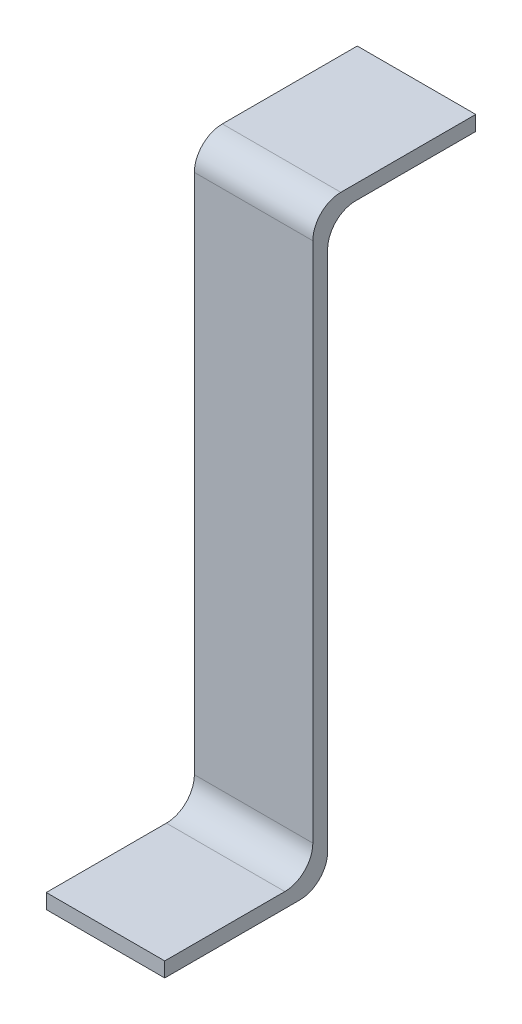
SolidWorks part; units mm, degrees
material "6061-T6 (SS)"
ref_plane "Front Plane" through (0, 0, 0) normal (0, 0, 1) x (1, 0, 0)
ref_plane "Top Plane" through (0, 0, 0) normal (0, 1, 0) x (1, 0, 0)
ref_plane "Right Plane" through (0, 0, 0) normal (1, 0, 0) x (0, 0, -1)
sketch "Sketch1" plane through (0, 0, 0) normal (1, 0, 0) x (0, 0, -1)
  line L0 (1.4125, 63.5) -> (15.875, 63.5)
  line L1 (15.875, 63.5) -> (15.875, 61.9125)
  line L2 (15.875, 61.9125) -> (3, 61.9125)
  line L3 (0, 58.9125) -> (0, 3)
  line L4 (-3, 0) -> (-17.4625, 0)
  line L5 (-17.4625, 0) -> (-17.4625, 1.5875)
  line L6 (-17.4625, 1.5875) -> (-4.5875, 1.5875)
  line L7 (-1.5875, 4.5875) -> (-1.5875, 60.5)
  arc A0 (1.4125, 63.5) -> (-1.5875, 60.5) centre (1.4125, 60.5) ccw
  arc A1 (3, 61.9125) -> (0, 58.9125) centre (3, 58.9125) ccw
  arc A2 (0, 3) -> (-3, 0) centre (-3, 3) cw
  arc A3 (-4.5875, 1.5875) -> (-1.5875, 4.5875) centre (-4.5875, 4.5875) ccw
  point P11 (-1.5875, 63.5)
  point P16 (0, 0)
  dimension "D5" = 3
  dimension "D1" = 17.4625
  dimension "D2" = 17.4625
  dimension "D3" = 1.5875
  dimension "D4" = 1.5875
  dimension "D6" = 63.5
extrude "Boss-Extrude1" add sketch "Sketch1" along normal blind 12.7
